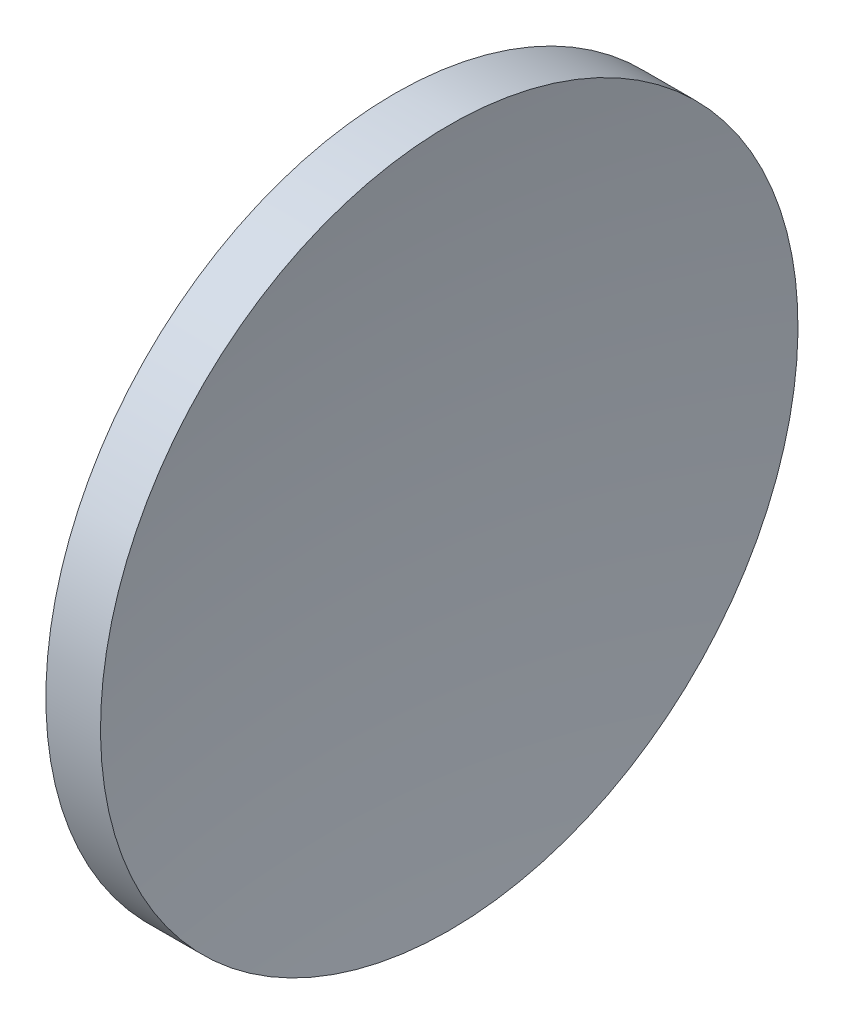
SolidWorks part; units mm, degrees
ref_plane "前视基准面" through (0, 0, 0) normal (0, 0, 1) x (1, 0, 0)
ref_plane "上视基准面" through (0, 0, 0) normal (0, 1, 0) x (1, 0, 0)
ref_plane "右视基准面" through (0, 0, 0) normal (1, 0, 0) x (0, 0, -1)
sketch "草图1" plane through (0, 0, 0) normal (0, 0, 1) x (1, 0, 0)
  line L0 (115.9445, 65.2168) -> (135.9482, 65.2168) construction
  line L1 (126.974, 84.2418) -> (129.9542, 84.2418)
  line L2 (128.4554, 65.2168) -> (122.8554, 65.2168)
  arc A0 (126.974, 84.2418) -> (122.8554, 65.2168) centre (168.8554, 65.2168) ccw
  arc A1 (129.9542, 84.2418) -> (128.4554, 65.2168) centre (249.9554, 65.2168) ccw
revolve "旋转1" add sketch "草图1" angle 360 about L0
